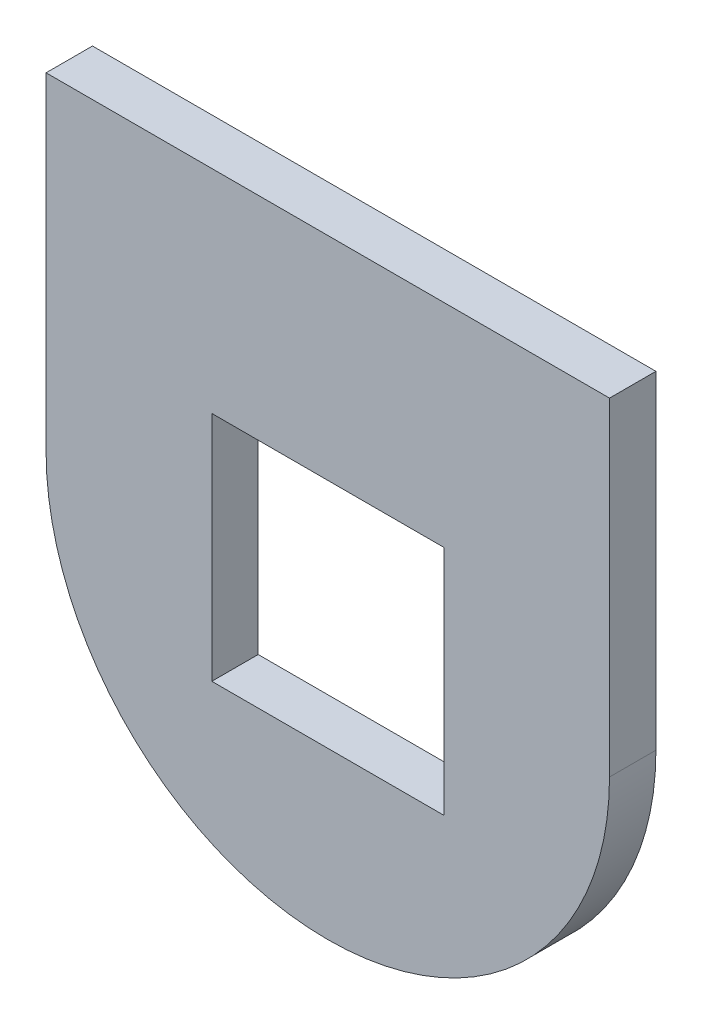
SolidWorks part; units mm, degrees
ref_plane "Front Plane" through (0, 0, 0) normal (0, 0, 1) x (1, 0, 0)
ref_plane "Top Plane" through (0, 0, 0) normal (0, 1, 0) x (1, 0, 0)
ref_plane "Right Plane" through (0, 0, 0) normal (1, 0, 0) x (0, 0, -1)
sketch "Sketch1" plane through (0, 0, 0) normal (0, 0, 1) x (1, 0, 0)
  line L1 (0, 0) -> (85, 0)
  line L2 (0, 0) -> (0, 95)
  line L3 (0, 95) -> (85, 95)
  line L4 (85, 0) -> (85, 95)
  dimension "D1" = 95
  dimension "D2" = 85
extrude "Boss-Extrude1" add sketch "Sketch1" along normal blind 7
sketch "Sketch2" plane through (0, 0, 7) normal (0, 0, 1) x (1, 0, 0)
  line L0 (0, 0) -> (85, 0) construction
  line L1 (25, 27.5) -> (60, 27.5)
  line L2 (25, 27.5) -> (25, 62.5)
  line L3 (25, 62.5) -> (60, 62.5)
  line L4 (60, 27.5) -> (60, 62.5)
  line L5 (25, 27.5) -> (60, 62.5) construction
  line L6 (25, 62.5) -> (60, 27.5) construction
  point P0 (42.5, 45)
  point P7 (42.5, 0)
  dimension "D1" = 0
  dimension "D2" = 35
  dimension "D3" = 35
  dimension "D4" = 45
extrude "Cut-Extrude1" cut sketch "Sketch2" against normal blind 7
sketch "Sketch4" plane through (0, 95, 0) normal (0, 1, 0) x (1, 0, 0)
  line L0 (0, -3.5) -> (85, -3.5) construction
  line L1 (0, -7) -> (0, 0) construction
  line L2 (85, -7) -> (85, 0) construction
  circle A0 centre (21.25, -3.5) radius 1.5
  circle A1 centre (63.75, -3.5) radius 1.5
  dimension "D1" = 3
  dimension "D2" = 3
  dimension "D3" = 21.25
  dimension "D4" = 21.25
sketch "Sketch6" plane through (0, 0, 0) normal (0, 0, -1) x (-1, 0, 0)
  line L0 (-85, 95) -> (0, 95) construction
  line L1 (-85, 0) -> (-85, 95) construction
  line L2 (-42.5, 62.5) -> (-42.5, 65.8033) construction
  line L3 (-60, 62.5) -> (-25, 62.5) construction
  line L4 (0, 95) -> (0, 0) construction
  line L5 (0, 0) -> (-85, 0) construction
  circle A0 centre (-80.75, 90.75) radius 1.5
  circle A1 centre (-4.25, 90.75) radius 1.5
  circle A2 centre (-4.45, 4.25) radius 1.5
  circle A3 centre (-80.75, 7.25) radius 1.5
  dimension "D1" = 3
  dimension "D5" = 3
  dimension "D7" = 3
  dimension "D2" = 4.25
  dimension "D3" = 4.25
  dimension "D4" = 4.45
  dimension "D6" = 4.25
  dimension "D8" = 7.25
  dimension "D9" = 4.25
sketch "Sketch7" plane through (0, 0, 0) normal (0, 0, -1) x (-1, 0, 0)
  line L0 (-85, 45) -> (-85, 0)
  line L1 (-85, 0) -> (0, 0)
  line L2 (0, 0) -> (0, 45)
  arc A0 (-85, 45) -> (0, 45) centre (-42.5, 45) ccw
  dimension "D1" = 85
extrude "Cut-Extrude4" cut sketch "Sketch7" against normal blind 10
sketch "Sketch8" plane through (0, 0, 7) normal (0, 0, 1) x (1, 0, 0)
  line L0 (85, 95) -> (0, 95) construction
  line L1 (85, 45) -> (85, 95) construction
  line L2 (42.5, 62.5) -> (42.5, 67.7032) construction
  line L3 (60, 62.5) -> (25, 62.5) construction
  circle A0 centre (80.75, 63) radius 1.5
  circle A1 centre (4.25, 63) radius 1.5
  dimension "D1" = 3
  dimension "D2" = 32
  dimension "D3" = 4.25
sketch "Sketch10" plane through (0, 0, 0) normal (0, 0, -1) x (-1, 0, 0)
  line L0 (-42.5, 2.5) -> (-42.5, 26.8409) construction
  arc A0 (-85, 45) -> (0, 45) centre (-42.5, 45) ccw construction
  circle A1 centre (-42.5, 6.75) radius 1.5
  dimension "D1" = 3
  dimension "D2" = 4.25
sketch "Sketch11" plane through (0, 0, 7) normal (0, 0, 1) x (1, 0, 0)
  circle A0 centre (42.5, 6.75) radius 1.5 construction
  circle A1 centre (42.5, 6.75) radius 1.5
sketch "Sketch12" plane through (0, 95, 0) normal (0, 1, 0) x (1, 0, 0)
  line L1 (0, -7) -> (85, -7)
  line L2 (0, -7) -> (0, 0)
  line L3 (0, 0) -> (85, 0)
  line L4 (85, -7) -> (85, 0)
extrude "Cut-Extrude9" cut sketch "Sketch12" against normal blind 0.5
